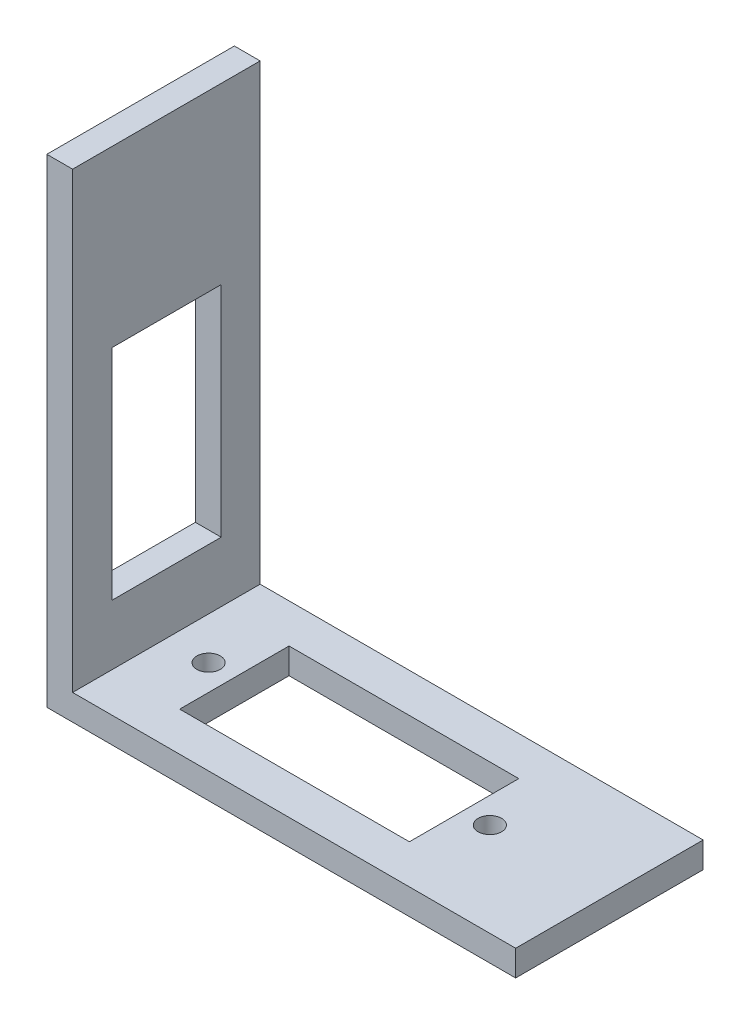
SolidWorks part; units mm, degrees
material "1060 Alloy"
ref_plane "Front Plane" through (0, 0, 0) normal (0, 0, 1) x (1, 0, 0)
ref_plane "Top Plane" through (0, 0, 0) normal (0, 1, 0) x (1, 0, 0)
ref_plane "Right Plane" through (0, 0, 0) normal (1, 0, 0) x (0, 0, -1)
sketch "Sketch1" plane through (0, 0, 0) normal (0, 1, 0) x (1, 0, 0)
  line L1 (-30, -12) -> (30, -12)
  line L2 (-30, -12) -> (-30, 12)
  line L3 (-30, 12) -> (30, 12)
  line L4 (30, -12) -> (30, 12)
  line L5 (-30, -12) -> (30, 12) construction
  line L6 (-30, 12) -> (30, -12) construction
  point P0 (0, 0)
  dimension "D1" = 60
  dimension "D2" = 24
extrude "Boss-Extrude1" add sketch "Sketch1" along normal blind 3.3
sketch "Sketch2" plane through (0, 0, 0) normal (0, 1, 0) x (1, 0, 0)
  line L0 (-30, -12) -> (30, -12) construction
  line L5 (-30, 12) -> (-30, -12)
  line L6 (-30, -12) -> (-26.7, -12)
  line L7 (-26.7, -12) -> (-26.7, 12)
  line L8 (30, 12) -> (-30, 12) construction
  line L9 (-26.7, 12) -> (-30, 12)
  dimension "D2" = 3.3
extrude "Boss-Extrude2" add sketch "Sketch2" along normal blind 61.3
sketch "Sketch7" plane through (0, 0, 0) normal (0, 1, 0) x (1, 0, 0)
  line L0 (-33, 0) -> (33, 0) construction
  line L1 (11.4, 7) -> (-18, 7)
  line L2 (11.4, 7) -> (11.4, -7)
  line L3 (11.4, -7) -> (-18, -7)
  line L4 (-18, 7) -> (-18, -7)
  line L5 (11.4, 7) -> (-18, -7) construction
  line L6 (11.4, -7) -> (-18, 7) construction
  line L7 (-3.3, 7) -> (-3.3, -7) construction
  line L8 (-18, 0) -> (11.4, 0) construction
  line L9 (-30, 12) -> (-30, -12) construction
  circle A0 centre (-21.3, 0) radius 1.5
  circle A1 centre (14.7, 0) radius 1.5
  dimension "D1" = 36
  dimension "D2" = 3
  dimension "D3" = 29.4
  dimension "D4" = 14
  dimension "D5" = 12
extrude "Cut-Extrude4" cut sketch "Sketch7" along normal up to surface (3.3 mm away) up to face at (1.65, 3.3, 0)
sketch "Sketch9" plane through (-30, 0, 0) normal (-1, 0, 0) x (0, 0, 1)
  line L0 (-12, 0) -> (12, 0) construction
  line L1 (6.9872, 11) -> (-7.0128, 11)
  line L2 (6.9872, 11) -> (6.9872, 39)
  line L3 (6.9872, 39) -> (-7.0128, 39)
  line L4 (-7.0128, 11) -> (-7.0128, 39)
  line L5 (6.9872, 11) -> (-7.0128, 39) construction
  line L6 (6.9872, 39) -> (-7.0128, 11) construction
  point P0 (-0.0128, 25)
  point P7 (0, 0)
  dimension "D1" = 14
  dimension "D2" = 28
  dimension "D3" = 25
extrude "Cut-Extrude5" cut sketch "Sketch9" against normal blind 10
